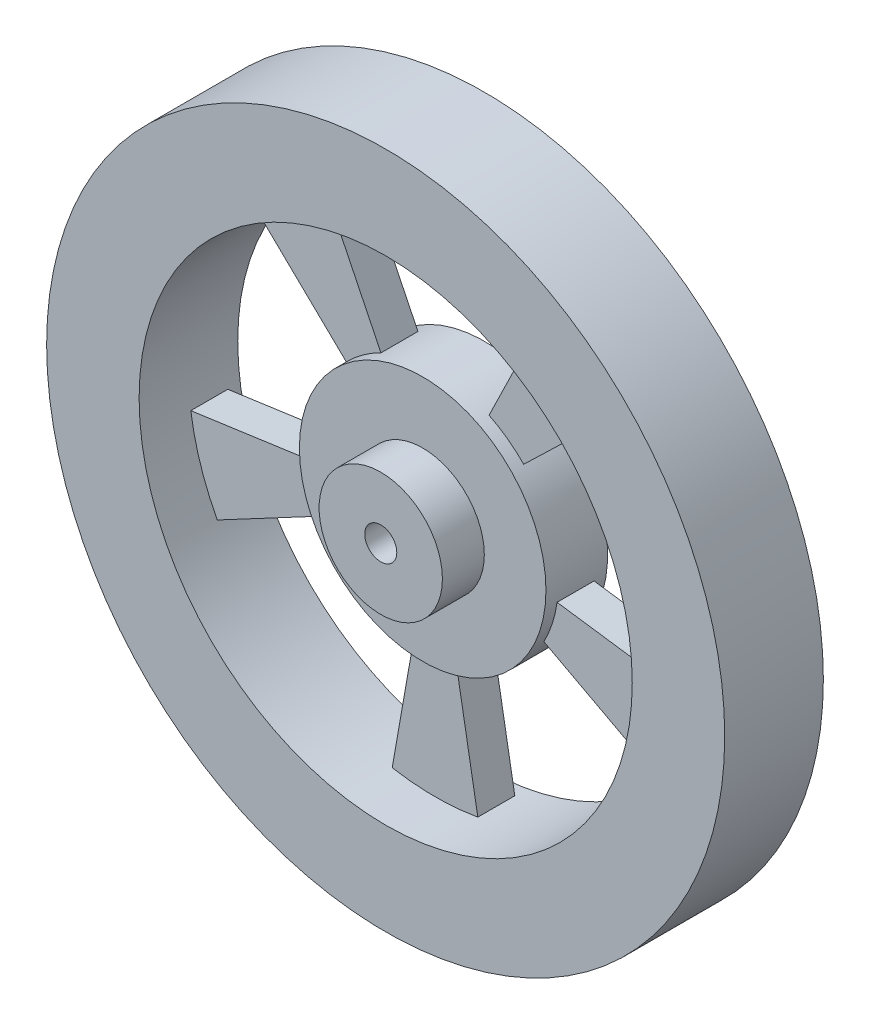
SolidWorks part; units mm, degrees
ref_plane "Front Plane" through (0, 0, 0) normal (0, 0, 1) x (1, 0, 0)
ref_plane "Top Plane" through (0, 0, 0) normal (0, 1, 0) x (1, 0, 0)
ref_plane "Right Plane" through (0, 0, 0) normal (1, 0, 0) x (0, 0, -1)
sketch "Sketch1" plane through (0, 0, 0) normal (0, 0, 1) x (1, 0, 0)
  circle A0 centre (0, 0) radius 17.4625
extrude "Boss-Extrude1" add sketch "Sketch1" along normal blind 5.08
sketch "Sketch2" plane through (0, 0, 0) normal (0, 0, -1) x (-1, 0, 0)
  line L1 (2.2053, -12.5071) -> (1.1027, -6.2535)
  line L2 (-1.1027, -6.2535) -> (-2.2053, -12.5071)
  line L3 (-6.2882, -0.8837) -> (-12.5764, -1.7675)
  line L4 (-11.2134, -5.9623) -> (-5.6067, -2.9811)
  line L5 (-2.7837, 5.7073) -> (-5.5673, 11.4147)
  line L6 (-9.1356, 8.8222) -> (-4.5678, 4.4111)
  line L7 (4.5678, 4.4111) -> (9.1356, 8.8222)
  line L8 (5.5673, 11.4147) -> (2.7837, 5.7073)
  line L9 (5.6067, -2.9811) -> (11.2134, -5.9623)
  line L10 (12.5764, -1.7675) -> (6.2882, -0.8837)
  arc A0 (6.2882, -0.8837) -> (4.5678, 4.4111) centre (0, 0) ccw
  arc A1 (12.5764, -1.7675) -> (9.1356, 8.8222) centre (0, 0) ccw
  arc A3 (1.1027, -6.2535) -> (5.6067, -2.9811) centre (0, 0) ccw
  arc A4 (2.2053, -12.5071) -> (11.2134, -5.9623) centre (0, 0) ccw
  arc A5 (-11.2134, -5.9623) -> (-2.2053, -12.5071) centre (0, 0) ccw
  arc A6 (-5.6067, -2.9811) -> (-1.1027, -6.2535) centre (0, 0) ccw
  arc A7 (-4.5678, 4.4111) -> (-6.2882, -0.8837) centre (0, 0) ccw
  arc A8 (-9.1356, 8.8222) -> (-12.5764, -1.7675) centre (0, 0) ccw
  arc A9 (5.5673, 11.4147) -> (-5.5673, 11.4147) centre (0, 0) ccw
  arc A10 (2.7837, 5.7073) -> (-2.7837, 5.7073) centre (0, 0) ccw
  point P30 (0, 0)
  dimension "D3" = 5
extrude "Cut-Extrude1" cut sketch "Sketch2" against normal blind 5.08
sketch "Sketch3" plane through (0, 0, 5.08) normal (0, 0, 1) x (1, 0, 0)
  circle A0 centre (0, 0) radius 3.175
extrude "Boss-Extrude2" add sketch "Sketch3" along normal blind 0.254
sketch "Sketch4" plane through (0, 0, 5.334) normal (0, 0, 1) x (1, 0, 0)
  circle A0 centre (0, 0) radius 0.8255
extrude "Cut-Extrude2" cut sketch "Sketch4" against normal through all
sketch "Sketch5" plane through (0, 0, 5.08) normal (0, 0, 1) x (1, 0, 0)
  circle A0 centre (0, 0) radius 12.7
  circle A1 centre (0, 0) radius 6.35
extrude "Cut-Extrude3" cut sketch "Sketch5" against normal blind 2.54
sketch "Sketch6" plane through (0, 0, 0) normal (0, 0, -1) x (-1, 0, 0)
  circle A0 centre (0, 0) radius 12.7
  circle A1 centre (0, 0) radius 6.35
extrude "Cut-Extrude4" cut sketch "Sketch6" against normal blind 0.635
sketch "Sketch7" plane through (0, 0, 5.08) normal (0, 0, 1) x (1, 0, 0)
  circle A0 centre (0, 0) radius 6.35
  circle A1 centre (0, 0) radius 3.175
extrude "Cut-Extrude5" cut sketch "Sketch7" against normal blind 1.905
